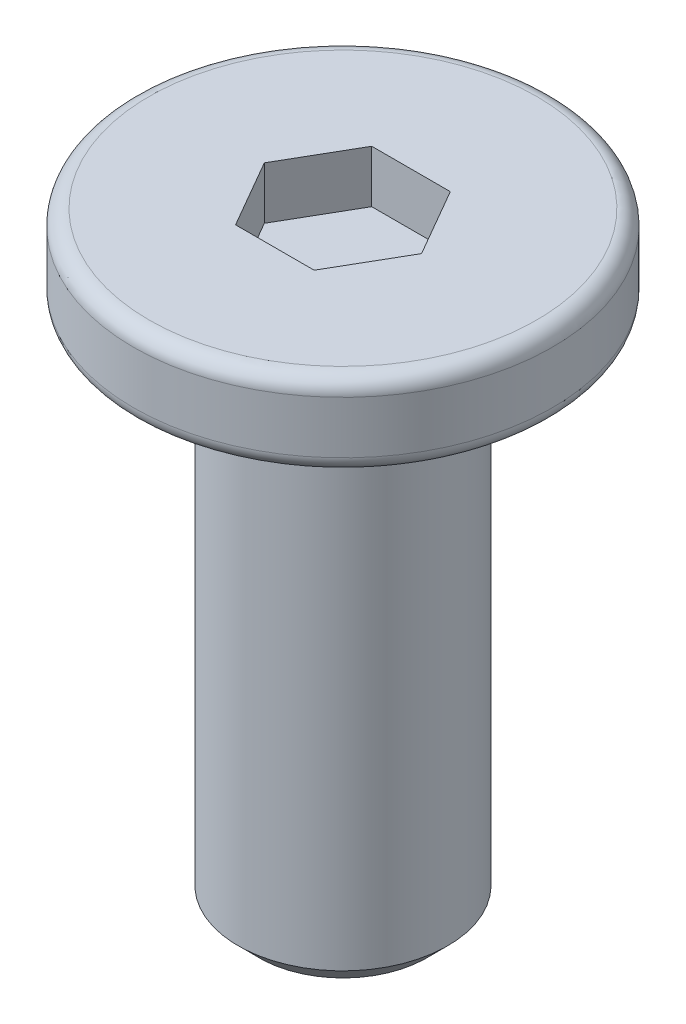
SolidWorks part; units mm, degrees
ref_plane "前视基准面" through (0, 0, 0) normal (0, 0, 1) x (1, 0, 0)
ref_plane "上视基准面" through (0, 0, 0) normal (0, 1, 0) x (1, 0, 0)
ref_plane "右视基准面" through (0, 0, 0) normal (1, 0, 0) x (0, 0, -1)
sketch "草图1" plane through (0, 0, 0) normal (0, 1, 0) x (1, 0, 0)
  circle A0 centre (0, 0) radius 2
  dimension "D1" = 4
extrude "凸台-拉伸1" add sketch "草图1" along normal blind 0.8
sketch "草图2" plane through (0, 0, 0) normal (0, -1, 0) x (1, 0, 0)
  circle A0 centre (0, 0) radius 1
  dimension "D1" = 2
extrude "凸台-拉伸2" add sketch "草图2" along normal blind 5
fillet "圆角1" radius 0.15 2 edges at (0, 0, 2) (0, 0.8, 2)
chamfer "倒角1" distance 0.2 angle 45 1 edges at (0, -5, -1)
sketch "草图3" plane through (0, 0.8, 0) normal (0, 1, 0) x (1, 0, 0)
  line L1 (0.7506, 0) -> (0.3753, 0.65)
  line L2 (0.3753, 0.65) -> (-0.3753, 0.65)
  line L3 (-0.3753, 0.65) -> (-0.7506, 0)
  line L4 (-0.7506, 0) -> (-0.3753, -0.65)
  line L5 (-0.3753, -0.65) -> (0.3753, -0.65)
  line L6 (0.3753, -0.65) -> (0.7506, 0)
  circle A0 centre (0, 0) radius 0.65 construction
  dimension "D1" = 1.3
extrude "切除-拉伸1" cut sketch "草图3" against normal blind 0.5
